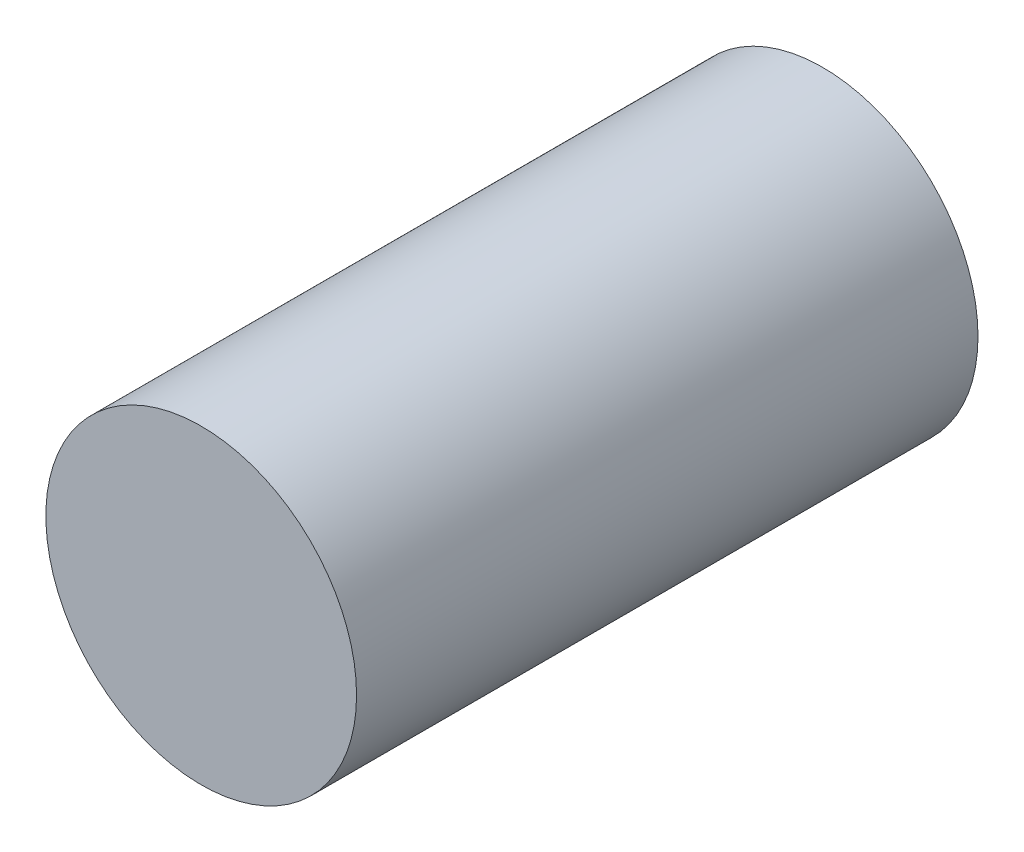
SolidWorks part; units mm, degrees
material "ABS"
ref_plane "Plan de face" through (0, 0, 0) normal (0, 0, 1) x (1, 0, 0)
ref_plane "Plan de dessus" through (0, 0, 0) normal (0, 1, 0) x (1, 0, 0)
ref_plane "Plan de droite" through (0, 0, 0) normal (1, 0, 0) x (0, 0, -1)
sketch "Esquisse1" plane through (0, 0, 0) normal (0, 0, 1) x (1, 0, 0)
  circle A0 centre (0, 0) radius 4
  dimension "D1" = 8
extrude "Boss.-Extru.1" add sketch "Esquisse1" along normal blind 16
